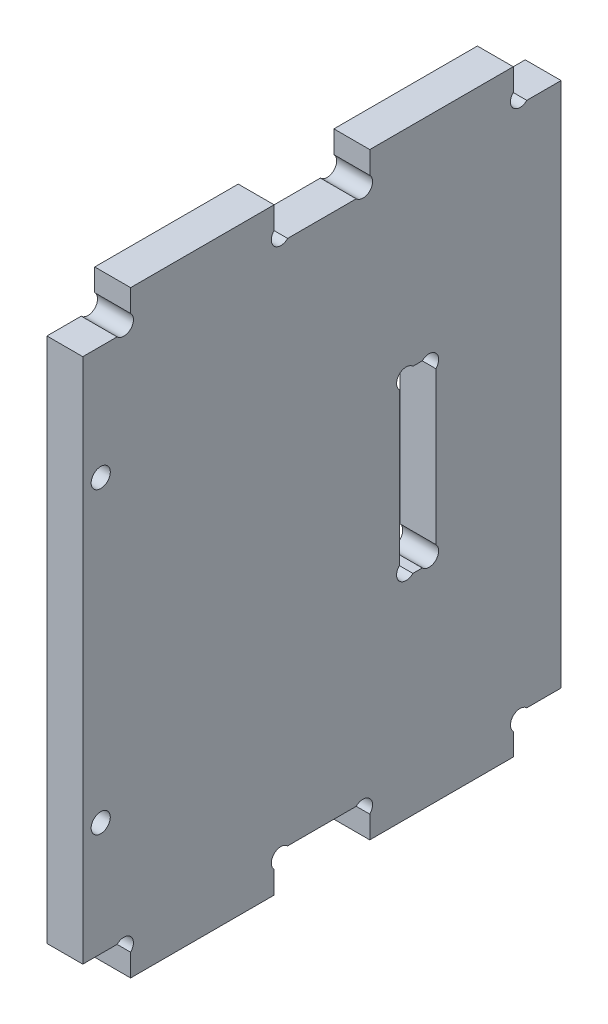
SolidWorks part; units mm, degrees
ref_plane "Plan de face" through (0, 0, 0) normal (0, 0, 1) x (1, 0, 0)
ref_plane "Plan de dessus" through (0, 0, 0) normal (0, 1, 0) x (1, 0, 0)
ref_plane "Plan de droite" through (0, 0, 0) normal (1, 0, 0) x (0, 0, -1)
sketch "Esquisse1" plane through (0, 0, 0) normal (1, 0, 0) x (0, 0, -1)
  line L0 (40, 114.5511) -> (40, -14.9803) construction
  line L1 (0, 0) -> (80, 0) construction
  line L2 (0, 0) -> (0, 100) construction
  line L3 (0, 100) -> (80, 100) construction
  line L4 (80, 0) -> (80, 100) construction
  line L5 (-10.7408, 94) -> (90.0863, 94) construction
  line L6 (-25.6937, 50) -> (88.3435, 50) construction
  line L7 (8, 104.227) -> (8, 91.468) construction
  line L8 (32, 104.227) -> (32, 91.468) construction
  line L9 (20, 96.861) -> (20, 92.3626) construction
  line L10 (8, 94) -> (-4.2853, 106.2853) construction
  line L11 (0, 94) -> (5.7373, 94)
  line L12 (8, 96.2627) -> (8, 100)
  line L13 (8, 100) -> (32, 100)
  line L14 (32, 100) -> (32, 96.2627)
  line L15 (48, 100) -> (48, 96.2627)
  line L16 (72, 100) -> (48, 100)
  line L17 (72, 96.2627) -> (72, 100)
  line L18 (80, 94) -> (74.2627, 94)
  line L19 (34.2627, 94) -> (45.7373, 94)
  line L20 (34.2627, 6) -> (45.7373, 6)
  line L21 (80, 6) -> (74.2627, 6)
  line L22 (72, 3.7373) -> (72, 0)
  line L23 (72, 0) -> (48, 0)
  line L24 (48, 0) -> (48, 3.7373)
  line L25 (32, 0) -> (32, 3.7373)
  line L26 (8, 0) -> (32, 0)
  line L27 (8, 3.7373) -> (8, 0)
  line L28 (0, 6) -> (5.7373, 6)
  line L29 (80, 94) -> (80, 6)
  line L30 (0, 6) -> (0, 94)
  line L31 (3, -3.2382) -> (3, 37.3765) construction
  line L32 (-12.9652, 25) -> (16.6332, 25) construction
  line L33 (56, 81.2087) -> (56, 13.6774) construction
  line L34 (52.95, 65) -> (58.4317, 59.5183) construction
  line L35 (69.9394, 35) -> (45.7373, 35) construction
  line L37 (52.95, 27.0352) -> (52.95, 68.593) construction
  line L38 (55.2127, 65) -> (56.7873, 65)
  line L39 (49.9026, 65) -> (68.3068, 65) construction
  line L40 (52.95, 62.7373) -> (52.95, 37.2627)
  line L41 (59.05, 67.4056) -> (59.05, 27.0352) construction
  line L42 (55.2127, 35) -> (56.7873, 35)
  line L43 (59.05, 62.7373) -> (59.05, 37.2627)
  arc A0 (5.7373, 94) -> (8, 96.2627) centre (6.8686, 95.1314) ccw
  arc A1 (34.2627, 94) -> (32, 96.2627) centre (33.1314, 95.1314) cw
  arc A2 (45.7373, 94) -> (48, 96.2627) centre (46.8686, 95.1314) ccw
  arc A3 (74.2627, 94) -> (72, 96.2627) centre (73.1314, 95.1314) cw
  arc A4 (74.2627, 6) -> (72, 3.7373) centre (73.1314, 4.8686) ccw
  arc A5 (45.7373, 6) -> (48, 3.7373) centre (46.8686, 4.8686) cw
  arc A6 (34.2627, 6) -> (32, 3.7373) centre (33.1314, 4.8686) ccw
  arc A7 (5.7373, 6) -> (8, 3.7373) centre (6.8686, 4.8686) cw
  circle A8 centre (3, 25) radius 1.6
  circle A9 centre (3, 75) radius 1.6
  arc A10 (55.2127, 65) -> (52.95, 62.7373) centre (54.0814, 63.8686) ccw
  arc A11 (56.7873, 65) -> (59.05, 62.7373) centre (57.9186, 63.8686) cw
  arc A12 (56.7873, 35) -> (59.05, 37.2627) centre (57.9186, 36.1314) ccw
  arc A13 (55.2127, 35) -> (52.95, 37.2627) centre (54.0814, 36.1314) cw
  dimension "D5" = 6
  dimension "D1" = 8
  dimension "D2" = 24
  dimension "D3" = 12
  dimension "D4" = 45
  dimension "D6" = 24
  dimension "D7" = 15
  dimension "D8" = 30
  dimension "D9" = 3.05
  dimension "D10" = 6.1
  dimension "D11" = 45
extrude "Extrusion1" add sketch "Esquisse1" along normal blind 6
